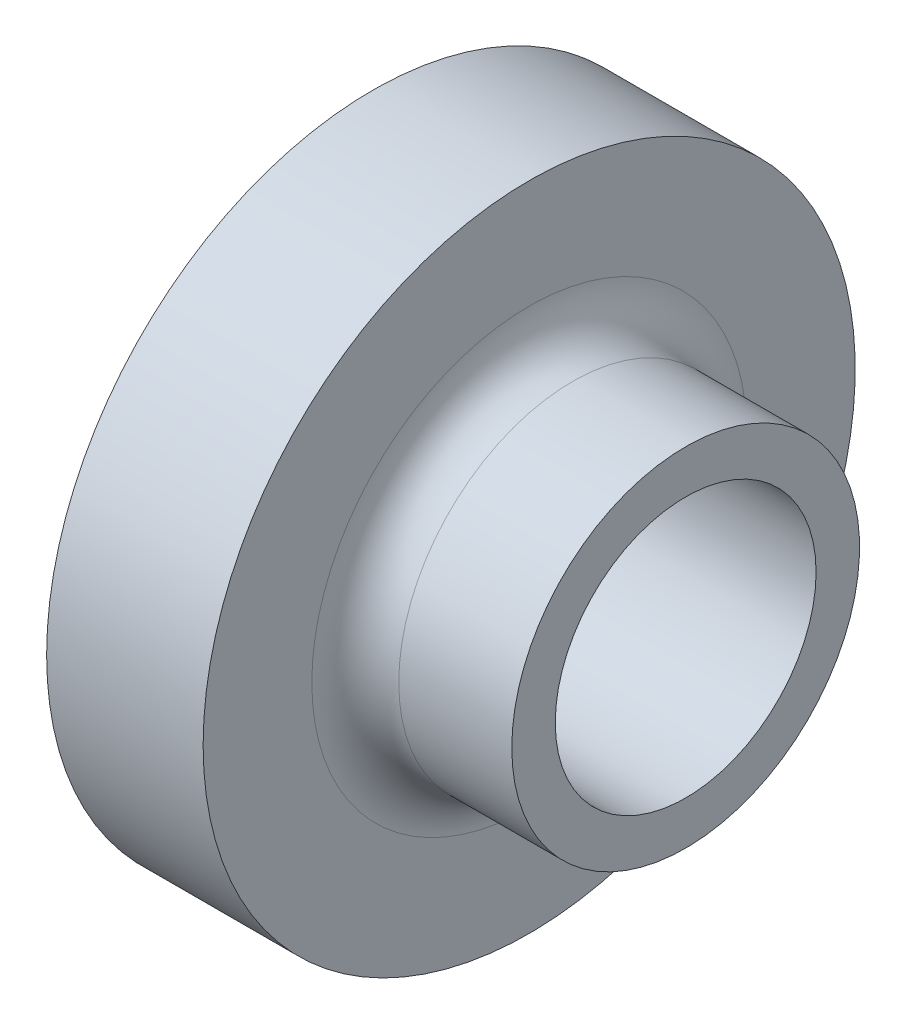
SolidWorks part; units mm, degrees
ref_plane "Front Plane" through (0, 0, 0) normal (0, 0, 1) x (1, 0, 0)
ref_plane "Top Plane" through (0, 0, 0) normal (0, 1, 0) x (1, 0, 0)
ref_plane "Right Plane" through (0, 0, 0) normal (1, 0, 0) x (0, 0, -1)
sketch "Çizim1" plane through (0, 0, 0) normal (0, 0, 1) x (1, 0, 0)
  line L6 (0, 37.5) -> (0, -37.5) construction
  line L7 (0, 37.5) -> (18, 37.5)
  line L8 (18, 37.5) -> (18, 20)
  line L9 (18, 20) -> (36, 20)
  line L10 (36, 20) -> (36, 15)
  line L11 (36, 15) -> (0, 15)
  line L12 (0, 15) -> (0, 37.5)
  line L13 (0, 0) -> (18, 0) construction
  point P4 (0, 0)
  dimension "D1" = 75
  dimension "D2" = 18
  dimension "D3" = 5
  dimension "D4" = 36
  dimension "D5" = 15
revolve "Döndür1" add sketch "Çizim1" angle 360 about L13
fillet "Radyus1" radius 5 1 edges at (18, 0, 20)
